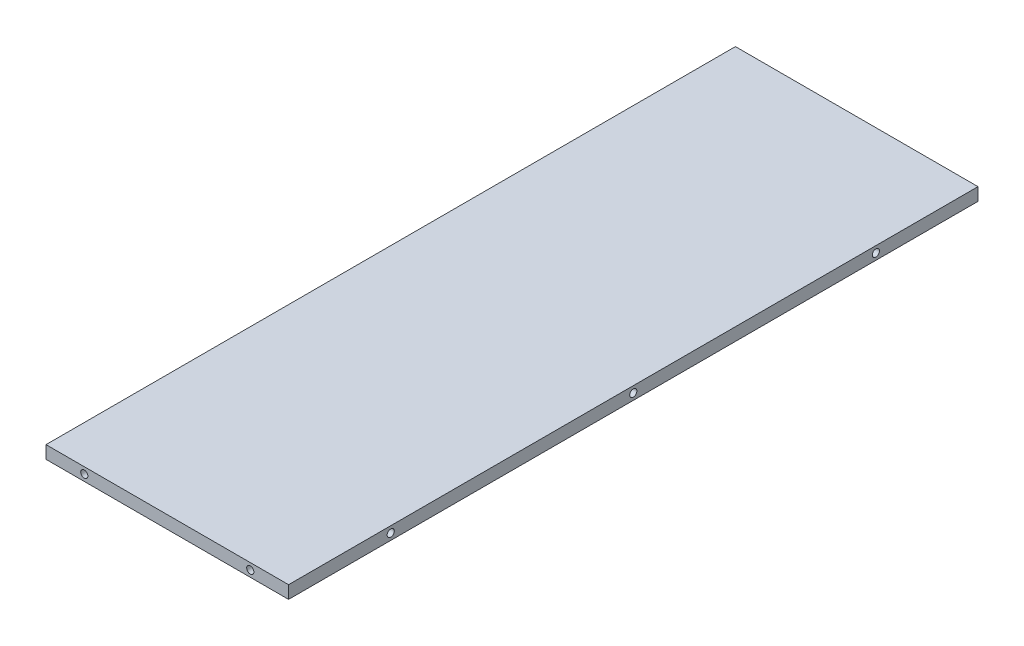
SolidWorks part; units mm, degrees
material "Delrin"
ref_plane "Front Plane" through (0, 0, 0) normal (0, 0, 1) x (1, 0, 0)
ref_plane "Top Plane" through (0, 0, 0) normal (0, 1, 0) x (1, 0, 0)
ref_plane "Right Plane" through (0, 0, 0) normal (1, 0, 0) x (0, 0, -1)
sketch "Sketch1" plane through (0, 0, 0) normal (0, 1, 0) x (1, 0, 0)
  line L1 (-30.1625, 85.725) -> (30.1625, 85.725)
  line L2 (-30.1625, 85.725) -> (-30.1625, -85.725)
  line L3 (-30.1625, -85.725) -> (30.1625, -85.725)
  line L4 (30.1625, 85.725) -> (30.1625, -85.725)
  dimension "D1" = 171.45
  dimension "D2" = 85.725
  dimension "D3" = 60.325
  dimension "D4" = 30.1625
extrude "Extrude1" add sketch "Sketch1" along normal blind 3.175
hole_wizard "Tap Drill for #2 Tap2" positions "3DSketch1" profile "Sketch2" hole size "#2-56" standard "Ansi Inch"
sketch3d "3DSketch1"
  line L0 (-30.1625, 3.175, 85.725) -> (30.1625, 3.175, 85.725) construction
  line L1 (30.1625, 3.175, 85.725) -> (30.1625, 0, 85.725) construction
  line L2 (-30.1625, 3.175, 85.725) -> (-30.1625, 0, 85.725) construction
  point P0 (-20.6375, 1.5875, 85.725)
  point P2 (20.6375, 1.5875, 85.725)
  dimension "D1" = 1.5875
  dimension "D2" = 1.5875
  dimension "D3" = 9.525
  dimension "D4" = 9.525
sketch "Sketch2" plane through (-20.6375, 1.5875, 85.725) normal (1, 0, 0) x (0, -1, 0)
  line L0 (0, 0) -> (0, 6.8842)
  line L1 (0, 6.8842) -> (0.889, 6.35)
  line L2 (0.889, 6.35) -> (0.889, 0)
  line L5 (0.889, 0) -> (0, 0)
  line L10 (0, 6.8842) -> (-0.889, 6.35) construction
  line L11 (0, -6.35) -> (0, 107.95) construction
  dimension "Hole Dia." = 1.778
  dimension "Hole Depth" = 6.35
  dimension "Drill Angle" = 118
hole_wizard "Tap Drill for #2 Tap4" positions "3DSketch4" profile "Sketch6" hole size "#2-56" standard "Ansi Inch"
sketch3d "3DSketch4"
  line L0 (30.1625, 3.175, -85.725) -> (-30.1625, 3.175, -85.725) construction
  line L1 (30.1625, 0, -85.725) -> (-30.1625, 0, -85.725) construction
  line L2 (-30.1625, 3.175, -85.725) -> (-30.1625, 0, -85.725) construction
  line L3 (30.1625, 3.175, -85.725) -> (30.1625, 0, -85.725) construction
  point P0 (20.6375, 1.5875, -85.725)
  point P2 (-20.6375, 1.5875, -85.725)
  dimension "D1" = 1.5875
  dimension "D2" = 1.5875
  dimension "D3" = 9.525
  dimension "D4" = 9.525
sketch "Sketch6" plane through (20.6375, 1.5875, -85.725) normal (1, 0, 0) x (0, 1, 0)
  line L0 (0, 0) -> (0, 6.8842)
  line L1 (0, 6.8842) -> (0.889, 6.35)
  line L2 (0.889, 6.35) -> (0.889, 0)
  line L5 (0.889, 0) -> (0, 0)
  line L10 (0, 6.8842) -> (-0.889, 6.35) construction
  line L11 (0, -6.35) -> (0, 107.95) construction
  dimension "Hole Dia." = 1.778
  dimension "Hole Depth" = 6.35
  dimension "Drill Angle" = 118
hole_wizard "Tap Drill for #2 Tap5" positions "3DSketch5" profile "Sketch7" hole size "#2-56" standard "Ansi Inch"
sketch3d "3DSketch5"
  line L1 (-30.1625, 3.175, -85.725) -> (-30.1625, 3.175, 85.725) construction
  line L2 (30.1625, 0, 85.725) -> (30.1625, 0, -85.725) construction
  line L3 (30.1625, 3.175, 85.725) -> (30.1625, 3.175, -85.725) construction
  line L4 (30.1625, 3.175, -85.725) -> (30.1625, 0, -85.725) construction
  line L5 (-30.1625, 3.175, -85.725) -> (-30.1625, 0, -85.725) construction
  line L6 (30.1625, 3.175, 85.725) -> (30.1625, 0, 85.725) construction
  line L7 (-30.1625, 3.175, 85.725) -> (-30.1625, 0, 85.725) construction
  point P0 (-30.1625, 1.5875, -60.325)
  point P4 (-30.1625, 1.5875, 60.325)
  point P6 (0, 0, 0)
  point P9 (30.1625, 1.5875, -60.325)
  point P15 (30.1625, 1.5875, 60.325)
  point P20 (30.1625, 1.5875, 0)
  point P22 (-30.1625, 1.5875, 0)
  dimension "D1" = 1.5875
  dimension "D2" = 1.5875
  dimension "D3" = 1.5875
  dimension "D4" = 1.5875
  dimension "D5" = 1.5875
  dimension "D6" = 1.5875
  dimension "D7" = 25.4
  dimension "D8" = 25.4
  dimension "D9" = 85.725
  dimension "D10" = 85.725
  dimension "D11" = 25.4
  dimension "D12" = 25.4
sketch "Sketch7" plane through (-30.1625, 1.5875, -60.325) normal (0, 1, 0) x (0, 0, 1)
  line L0 (0, 0) -> (0, 6.8842)
  line L1 (0, 6.8842) -> (0.889, 6.35)
  line L2 (0.889, 6.35) -> (0.889, 0)
  line L5 (0.889, 0) -> (0, 0)
  line L10 (0, 6.8842) -> (-0.889, 6.35) construction
  line L11 (0, -6.35) -> (0, 107.95) construction
  dimension "Hole Dia." = 1.778
  dimension "Hole Depth" = 6.35
  dimension "Drill Angle" = 118
